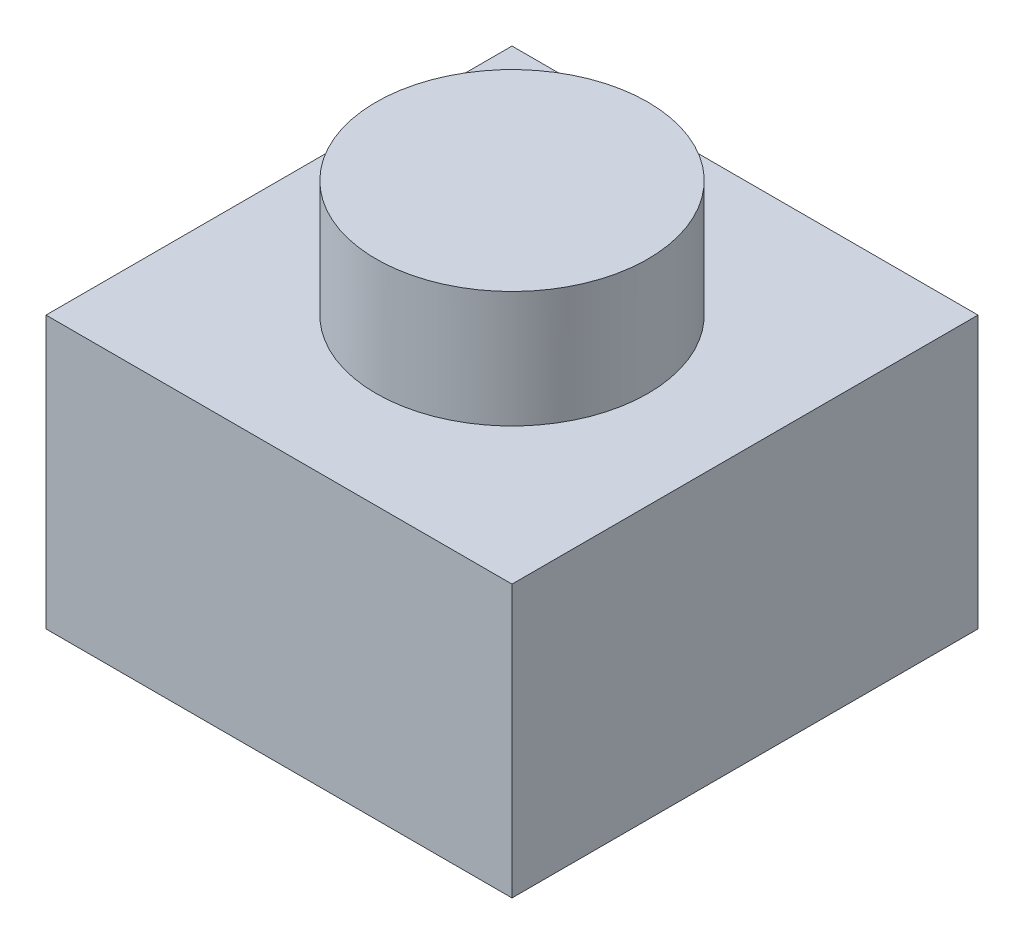
SolidWorks part; units mm, degrees
ref_plane "前视基准面" through (0, 0, 0) normal (0, 0, 1) x (1, 0, 0)
ref_plane "上视基准面" through (0, 0, 0) normal (0, 1, 0) x (1, 0, 0)
ref_plane "右视基准面" through (0, 0, 0) normal (1, 0, 0) x (0, 0, -1)
sketch "草图1" plane through (0, 0, 0) normal (0, 1, 0) x (1, 0, 0)
  line L1 (-3, 3) -> (3, 3)
  line L2 (-3, 3) -> (-3, -3)
  line L3 (-3, -3) -> (3, -3)
  line L4 (3, 3) -> (3, -3)
  line L5 (-3, 3) -> (3, -3) construction
  line L6 (-3, -3) -> (3, 3) construction
  point P0 (0, 0)
  dimension "D1" = 6
extrude "凸台-拉伸1" add sketch "草图1" along normal blind 3.5
sketch "草图2" plane through (0, 0, 0) normal (0, -1, 0) x (1, 0, 0)
  circle A0 centre (0, 0) radius 1.75
  dimension "D1" = 3.5
extrude "凸台-拉伸2" add sketch "草图2" against normal blind 5
